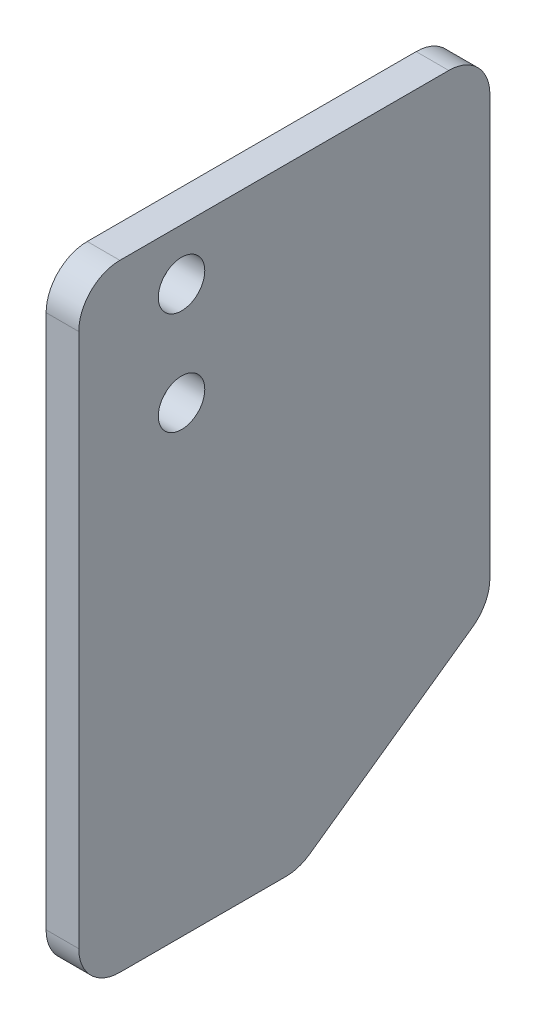
SolidWorks part; units mm, degrees
ref_plane "前视基准面" through (0, 0, 0) normal (0, 0, 1) x (1, 0, 0)
ref_plane "上视基准面" through (0, 0, 0) normal (0, 1, 0) x (1, 0, 0)
ref_plane "右视基准面" through (0, 0, 0) normal (1, 0, 0) x (0, 0, -1)
ref_plane "基准面4" through (-0.7938, 0, 0) normal (-1, 0, 0) x (0, -1, 0)
sketch "草图1" plane through (-0.7938, 0, 0) normal (-1, 0, 0) x (0, -1, 0)
  line L0 (40.795, -5.0783) -> (40.795, 3)
  line L1 (38.795, 5) -> (12.795, 5)
  line L2 (10.795, 3) -> (10.795, -13)
  line L3 (12.795, -15) -> (33.1935, -15)
  line L4 (34.8265, -14.1547) -> (40.428, -6.233)
  arc A0 (40.428, -6.233) -> (40.795, -5.0783) centre (38.795, -5.0783) ccw
  arc A1 (40.795, 3) -> (38.795, 5) centre (38.795, 3) ccw
  arc A2 (12.795, 5) -> (10.795, 3) centre (12.795, 3) ccw
  arc A3 (10.795, -13) -> (12.795, -15) centre (12.795, -13) ccw
  arc A4 (33.1935, -15) -> (34.8265, -14.1547) centre (33.1935, -13) ccw
  circle A5 centre (18.295, 0) radius 1.1303
  circle A6 centre (13.295, 0) radius 1.1303
extrude "凸台-拉伸1" add sketch "草图1" against normal blind 1.588
